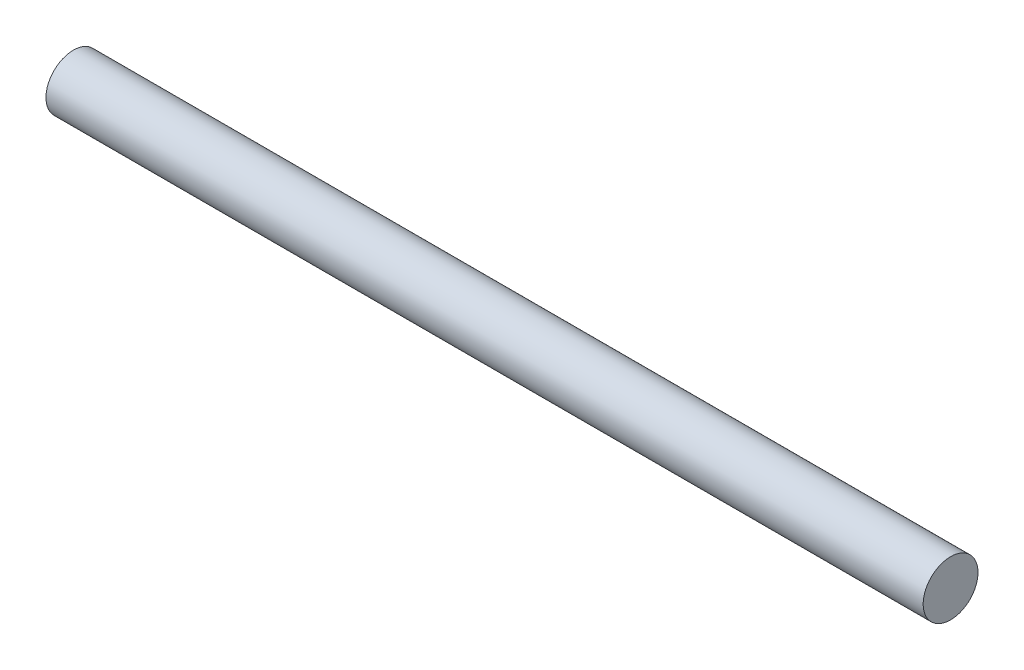
SolidWorks part; units mm, degrees
ref_plane "Front Plane" through (0, 0, 0) normal (0, 0, 1) x (1, 0, 0)
ref_plane "Top Plane" through (0, 0, 0) normal (0, 1, 0) x (1, 0, 0)
ref_plane "Right Plane" through (0, 0, 0) normal (1, 0, 0) x (0, 0, -1)
sketch "Sketch1" plane through (0, 0, 0) normal (1, 0, 0) x (0, 0, -1)
  circle A0 centre (0, 0) radius 0.25
  dimension "D1" = 0.5
extrude "Boss-Extrude1" add sketch "Sketch1" along normal blind 8
